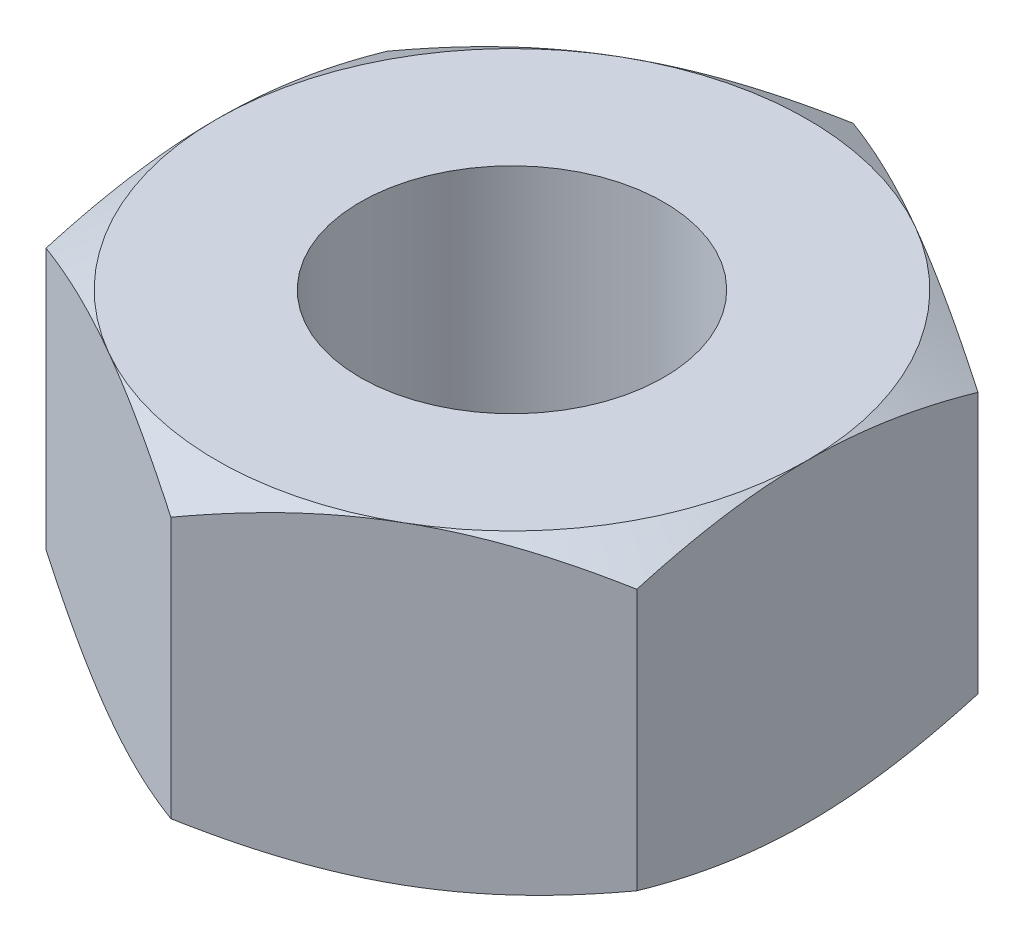
SolidWorks part; units mm, degrees
ref_plane "Front" through (0, 0, 0) normal (0, 0, 1) x (1, 0, 0)
ref_plane "Top" through (0, 0, 0) normal (0, 1, 0) x (1, 0, 0)
ref_plane "Right" through (0, 0, 0) normal (1, 0, 0) x (0, 0, -1)
sketch "Sketch1" plane through (0, 0, 0) normal (0, 1, 0) x (1, 0, 0)
  line L1 (6.35, -3.6662) -> (6.35, 3.6662)
  line L2 (6.35, 3.6662) -> (0, 7.3323)
  line L3 (0, 7.3323) -> (-6.35, 3.6662)
  line L4 (-6.35, 3.6662) -> (-6.35, -3.6662)
  line L5 (-6.35, -3.6662) -> (0, -7.3323)
  line L6 (0, -7.3323) -> (6.35, -3.6662)
  circle A0 centre (0, 0) radius 6.35 construction
  point P1 (0, 0.2887)
  dimension "D1" = 12.7
extrude "Boss-Extrude1" add sketch "Sketch1" along normal blind 3.3734 and the other way blind 3.3734
sketch "Sketch2" plane through (0, 3.3734, 0) normal (0, 1, 0) x (1, 0, 0)
  circle A0 centre (0, 0) radius 6.35
extrude "Cut-Extrude1" cut sketch "Sketch2" against normal through all draft 60 flip side to cut
mirror "Mirror1" about plane through (0, 0, 0) normal (0, 1, 0) of "Cut-Extrude1"
hole_wizard "5/16-18 Tapped Hole1" positions "Sketch3" profile "Sketch4" tap size "5/16-18" standard "ANSI Inch" end condition through all
sketch "Sketch3" plane through (0, 3.3734, 0) normal (0, 1, 0) x (1, 0, 0)
  point P0 (0, 0)
sketch "Sketch4" plane through (0, 3.3734, 0) normal (1, 0, 0) x (0, 0, 1)
  line L0 (0, 0) -> (0, 6.7469)
  line L1 (0, 6.7469) -> (3.2639, 6.7469)
  line L2 (3.2639, 6.7469) -> (3.2639, 0)
  line L5 (3.2639, 0) -> (0, 0)
  line L11 (0, -6.35) -> (0, 107.95) construction
  dimension "Thru Tap Drill Dia." = 6.5278
  dimension "Thru Tap Drill Depth" = 6.7469
cosmetic thread "Hole Thread1" parameters "D2"=7.9375
